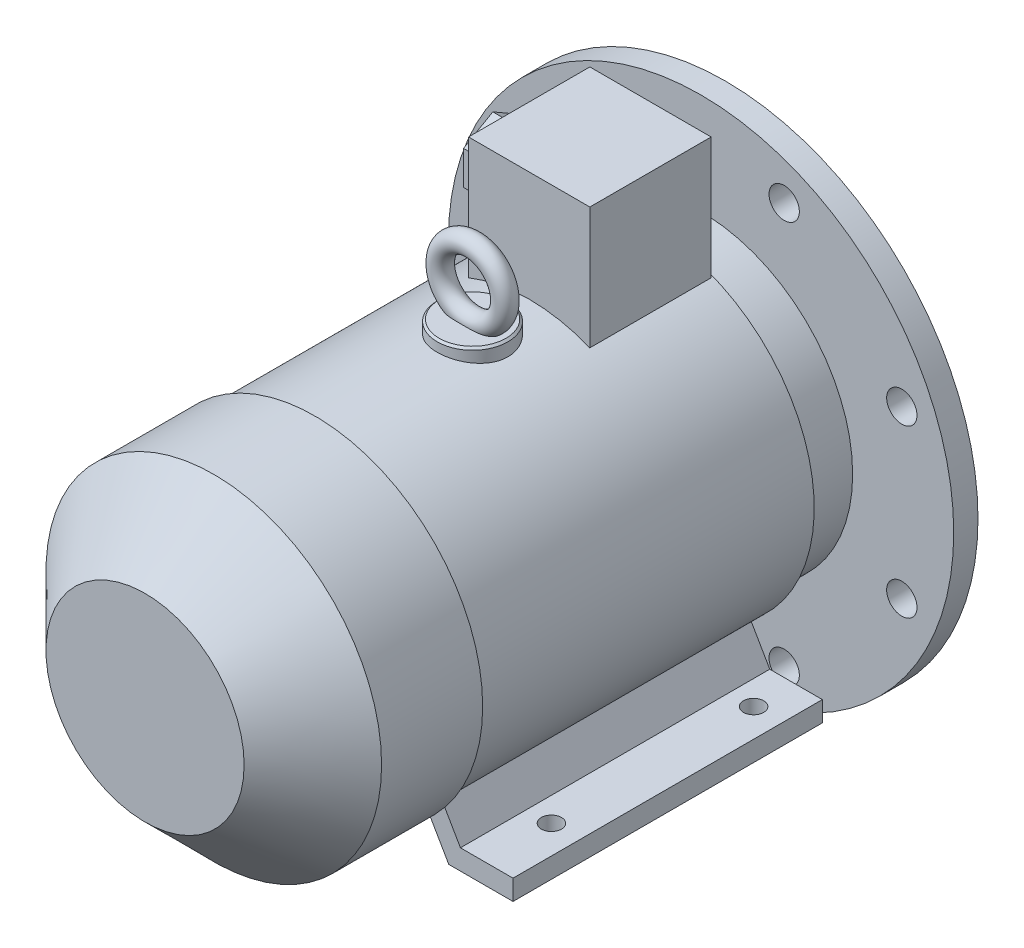
SolidWorks part; units mm, degrees
material "Ст.3 ГОСТ 380-88"
ref_plane "Спереди" through (0, 0, 0) normal (0, 0, 1) x (1, 0, 0)
ref_plane "Сверху" through (0, 0, 0) normal (0, 1, 0) x (1, 0, 0)
ref_plane "Справа" through (0, 0, 0) normal (1, 0, 0) x (0, 0, -1)
sketch "Эскиз1" plane through (0, 0, 0) normal (0, 0, 1) x (1, 0, 0)
  circle A0 centre (0, 0) radius 12
  dimension "D1" = 24
extrude "Вытянуть1" add sketch "Эскиз1" along normal blind 50
sketch "Эскиз2" plane through (0, 0, 0) normal (0, 0, -1) x (-1, 0, 0)
  line L0 (0, 0) -> (0, 14.6146) construction
  line L1 (-3.5, 15) -> (3.5, 15)
  line L2 (-3.5, 15) -> (-3.5, 8)
  line L3 (-3.5, 8) -> (3.5, 8)
  line L4 (3.5, 15) -> (3.5, 8)
  circle A1 centre (0, 0) radius 12 construction
  dimension "D1" = 7
  dimension "D2" = 7
  dimension "D3" = 27
extrude "Вытянуть2" add sketch "Эскиз2" against normal blind 25 and the other way blind 0.1
sketch "Эскиз3" plane through (0, 0, 50) normal (0, 0, 1) x (1, 0, 0)
  circle A0 centre (0, 0) radius 125
  dimension "D1" = 250
extrude "Вытянуть3" add sketch "Эскиз3" along normal blind 12
sketch "Эскиз4" plane through (0, 0, 50) normal (0, 0, -1) x (-1, 0, 0)
  circle A0 centre (0, 0) radius 90
  circle A2 centre (0, 0) radius 85
  dimension "D1" = 180
  dimension "D2" = 170
extrude "Вытянуть4" add sketch "Эскиз4" along normal blind 4
sketch "Эскиз5" plane through (0, 0, 50) normal (0, 0, -1) x (-1, 0, 0)
  circle A0 centre (0, 0) radius 85
  circle A1 centre (0, 0) radius 20
  dimension "D1" = 170
  dimension "D2" = 40
extrude "Вырез-Вытянуть1" cut sketch "Эскиз5" against normal blind 4
chamfer "Фаска1" distance 1 angle 45 3 edges at (-90, 0, 46) (-20, 0, 50) (0, -12, 0)
sketch "Эскиз6" plane through (0, 0, 50) normal (0, 0, -1) x (-1, 0, 0)
  line L0 (0, 0) -> (0, 145.4797) construction
  line L1 (0, 0) -> (-57.5388, 138.911) construction
  circle A0 centre (-41.1385, 99.317) radius 7.5
  circle A1 centre (41.1385, 99.317) radius 7.5
  circle A2 centre (99.317, 41.1385) radius 7.5
  circle A3 centre (99.317, -41.1385) radius 7.5
  circle A4 centre (41.1385, -99.317) radius 7.5
  circle A5 centre (-41.1385, -99.317) radius 7.5
  circle A6 centre (-99.317, -41.1385) radius 7.5
  circle A7 centre (-99.317, 41.1385) radius 7.5
  dimension "D2" = 15
  dimension "D1" = 22.5
  dimension "D3" = 107.5
  dimension "D4" = 107.5
  dimension "D5" = 107.5
extrude "Вырез-Вытянуть2" cut sketch "Эскиз6" against normal through all
sketch "Эскиз7" plane through (0, 0, 62) normal (0, 0, 1) x (1, 0, 0)
  circle A0 centre (0, 0) radius 75
  dimension "D1" = 150
extrude "Вытянуть5" add sketch "Эскиз7" along normal blind 24
sketch "Эскиз8" plane through (0, 0, 86) normal (0, 0, 1) x (1, 0, 0)
  circle A0 centre (0, 0) radius 80
  dimension "D1" = 160
extrude "Вытянуть6" add sketch "Эскиз8" along normal blind 167
sketch "Эскиз9" plane through (0, 0, 253) normal (0, 0, 1) x (1, 0, 0)
  circle A0 centre (0, 0) radius 83
  dimension "D1" = 166
extrude "Вытянуть7" add sketch "Эскиз9" along normal blind 84
chamfer "Фаска2" distance 34 angle 45 1 edges at (83, 0, 337)
sketch "Эскиз10" plane through (0, 0, 86) normal (0, 0, -1) x (-1, 0, 0)
  line L0 (0, 0) -> (0, -154.6475) construction
  line L1 (-84, -90) -> (-52.2265, -90)
  line L2 (-52.2265, -90) -> (-38.6255, -66.4424)
  line L3 (-84, -90) -> (-84, -80)
  line L4 (-84, -80) -> (-58, -80)
  line L5 (-58, -80) -> (-46.977, -60.9076)
  line L6 (-46.977, -60.9076) -> (-38.6255, -66.4424)
  line L7 (84, -90) -> (84, -80)
  line L8 (84, -90) -> (52.2265, -90)
  line L9 (52.2265, -90) -> (38.6255, -66.4424)
  line L10 (46.977, -60.9076) -> (38.6255, -66.4424)
  line L11 (58, -80) -> (46.977, -60.9076)
  line L12 (84, -80) -> (58, -80)
  dimension "D1" = 10
  dimension "D2" = 84
  dimension "D3" = 10
  dimension "D4" = 30
  dimension "D5" = 90
  dimension "D6" = 58
extrude "Вытянуть8" add sketch "Эскиз10" against normal blind 153
sketch "Эскиз11" plane through (0, -90, 0) normal (0, -1, 0) x (1, 0, 0)
  line L0 (118.9025, 106) -> (-128.9577, 106) construction
  line L2 (0, 0) -> (0, 348.6891) construction
  line L3 (-70, 106) -> (70, 106) construction
  line L4 (-70, 106) -> (-70, 206) construction
  circle A0 centre (-70, 106) radius 5
  circle A1 centre (70, 106) radius 5
  circle A2 centre (-70, 206) radius 5
  circle A3 centre (70, 206) radius 5
  dimension "D2" = 10
  dimension "D1" = 106
  dimension "D3" = 70
  dimension "D4" = 90
  dimension "D5" = 100
  dimension "D6" = 206
  dimension "D7" = 140
extrude "Вырез-Вытянуть3" cut sketch "Эскиз11" against normal up to next
sketch "Эскиз12" plane through (0, 0, 0) normal (0, 1, 0) x (1, 0, 0)
  line L0 (0, 0) -> (0, -360.711) construction
  line L1 (-30, -87) -> (30, -87)
  line L2 (-30, -87) -> (-30, -147)
  line L3 (-30, -147) -> (30, -147)
  line L4 (30, -87) -> (30, -147)
  line L6 (80, -86) -> (-80, -86) construction
  dimension "D1" = 60
  dimension "D2" = 60
  dimension "D3" = 1
extrude "Вытянуть9" add sketch "Эскиз12" along normal blind 134.5
sketch "Эскиз13" plane through (0, 0, 0) normal (0, 1, 0) x (1, 0, 0)
  line L0 (0, 0) -> (0, -243.5977) construction
  circle A0 centre (0, -175) radius 17.5
  dimension "D1" = 35
  dimension "D2" = 175
extrude "Вытянуть10" add sketch "Эскиз13" along normal blind 85.5
chamfer "Фаска3" distance 1 angle 45 1 edges at (0, 85.5, 192.5)
ref_plane "Плоскость1" through (0, 0, 175) normal (0, 0, 1) x (1, 0, 0)
sketch "Эскиз14" plane through (0, 0, 175) normal (0, 0, 1) x (1, 0, 0)
  line L0 (16.5, 85.5) -> (-16.5, 85.5) construction
  line L1 (0, 0) -> (0, 179.6737) construction
  circle A0 centre (0, 101.5) radius 16
  dimension "D1" = 32
sketch "Эскиз15" plane through (0, 0, 0) normal (1, 0, 0) x (0, 0, -1)
  line L0 (-175, 117.5) -> (-175, 85.5) construction
  line L1 (-158.5, 85.5) -> (-191.5, 85.5) construction
  circle A0 centre (-175, 117.5) radius 5
  dimension "D1" = 10
  dimension "D2" = 32
sweep "По траектории1" add profiles "Эскиз15" path "Эскиз14"
sketch "Эскиз16" plane through (-30, 0, 0) normal (-1, 0, 0) x (0, 0, 1)
  line L0 (87, 134.5) -> (87, 74.162) construction
  line L1 (87, 134.5) -> (147, 134.5) construction
  circle A0 centre (117, 104.5) radius 9
  dimension "D1" = 30
  dimension "D3" = 18
  dimension "D2" = 30
extrude "Вытянуть11" add sketch "Эскиз16" along normal blind 8
sketch "Эскиз17" plane through (-38, 0, 0) normal (-1, 0, 0) x (0, 0, 1)
  line L1 (117, 121.2432) -> (102.5, 112.8716)
  line L2 (102.5, 112.8716) -> (102.5, 96.1284)
  line L3 (102.5, 96.1284) -> (117, 87.7568)
  line L4 (117, 87.7568) -> (131.5, 96.1284)
  line L5 (131.5, 96.1284) -> (131.5, 112.8716)
  line L6 (131.5, 112.8716) -> (117, 121.2432)
  line L7 (117, 104.5) -> (117, 137.467) construction
  circle A0 centre (117, 104.5) radius 14.5 construction
  circle A1 centre (117, 104.5) radius 9 construction
  dimension "D1" = 29
extrude "Вытянуть12" add sketch "Эскиз17" along normal blind 10
sketch "Эскиз18" plane through (-48, 0, 0) normal (-1, 0, 0) x (0, 0, 1)
  circle A0 centre (117, 104.5) radius 6
  circle A1 centre (117, 104.5) radius 9 construction
  dimension "D1" = 12
extrude "Вырез-Вытянуть4" cut sketch "Эскиз18" against normal blind 10
